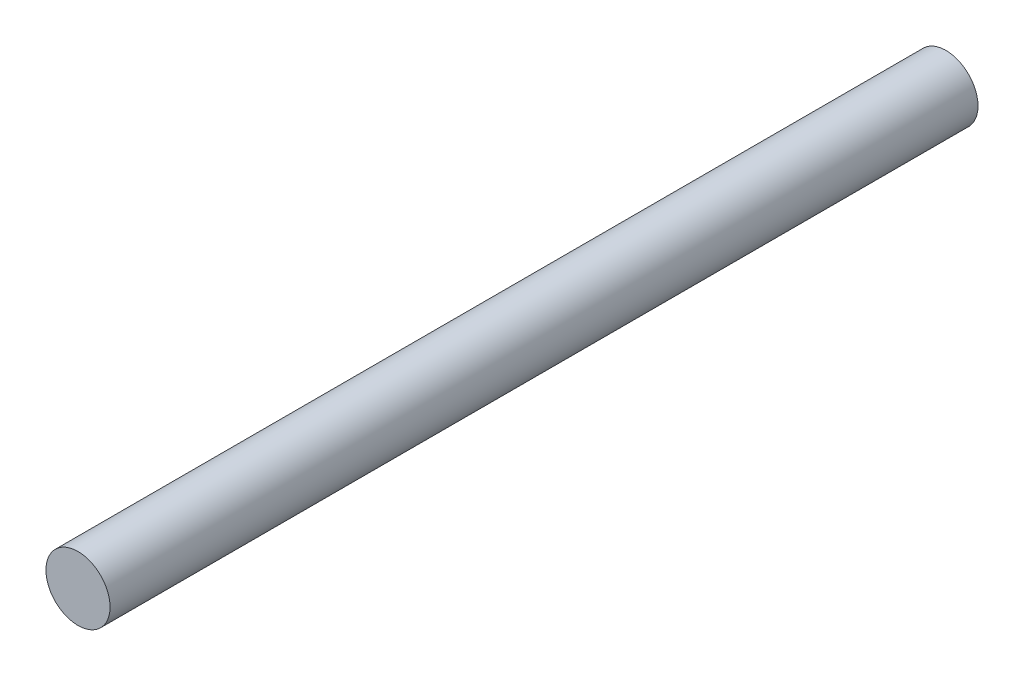
SolidWorks part; units mm, degrees
ref_plane "Front Plane" through (0, 0, 0) normal (0, 0, 1) x (1, 0, 0)
ref_plane "Top Plane" through (0, 0, 0) normal (0, 1, 0) x (1, 0, 0)
ref_plane "Right Plane" through (0, 0, 0) normal (1, 0, 0) x (0, 0, -1)
sketch "Sketch1" plane through (0, 0, 0) normal (0, 0, 1) x (1, 0, 0)
  circle A0 centre (0, 0) radius 5.8
extrude "Boss-Extrude1" add sketch "Sketch1" along normal blind 157 contours A0
